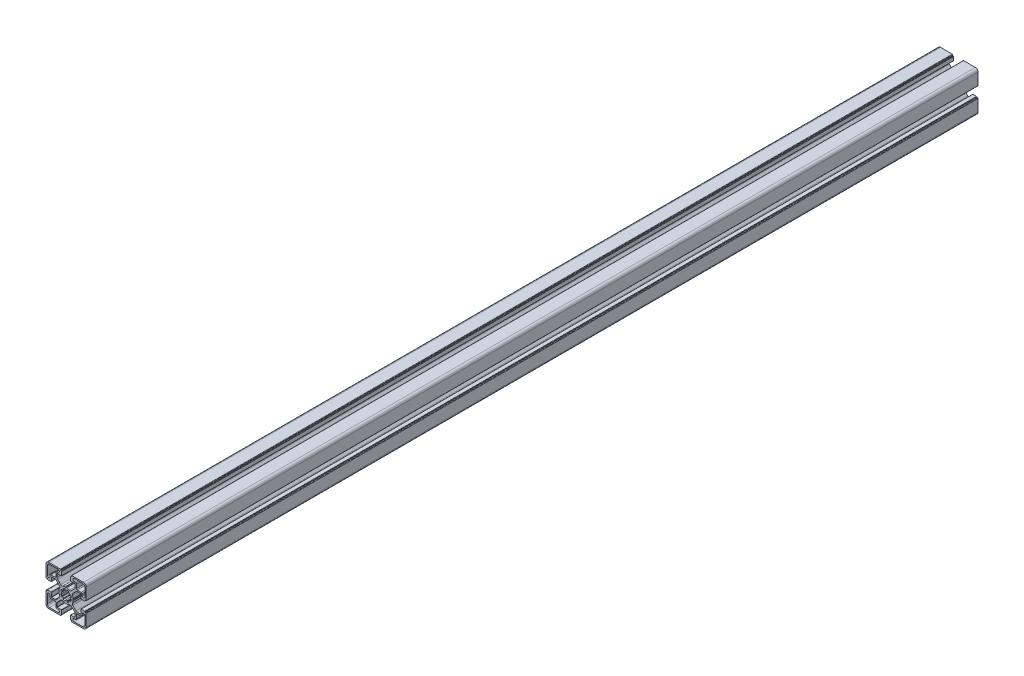
SolidWorks part; units mm, degrees
ref_plane "Plan de face" through (0, 0, 0) normal (0, 0, 1) x (1, 0, 0)
ref_plane "Plan de dessus" through (0, 0, 0) normal (0, 1, 0) x (1, 0, 0)
ref_plane "Plan de droite" through (0, 0, 0) normal (1, 0, 0) x (0, 0, -1)
sketch "Esquisse2" plane through (0, 0, 0) normal (0, 0, 1) x (1, 0, 0)
  line L28 (-195.0842, -352.0697) -> (-194.515, -352.1681)
  line L29 (-195.438, -354.39) -> (-195.9151, -354.0583)
  line L30 (-197.1408, -355.2803) -> (-196.8135, -355.7444)
  line L31 (-199.0372, -356.663) -> (-199.1374, -356.106)
  line L36 (-195.0842, -350.294) -> (-194.515, -350.1956)
  line L37 (-195.438, -347.9737) -> (-195.9151, -348.3053)
  line L38 (-197.1408, -347.0834) -> (-196.8135, -346.6192)
  line L39 (-199.0372, -345.7007) -> (-199.1374, -346.2577)
  line L40 (-200.9723, -356.663) -> (-200.8722, -356.106)
  line L41 (-202.8688, -355.2803) -> (-203.1961, -355.7444)
  line L42 (-204.5715, -354.39) -> (-204.0945, -354.0583)
  line L43 (-204.9253, -352.0697) -> (-205.4945, -352.1681)
  line L44 (-204.9253, -350.294) -> (-205.4945, -350.1956)
  line L45 (-204.5715, -347.9737) -> (-204.0945, -348.3053)
  line L46 (-202.8688, -347.0834) -> (-203.1961, -346.6192)
  line L47 (-200.9723, -345.7007) -> (-200.8722, -346.2577)
  line L105 (-200.0048, -338.2818) -> (-200.0048, -369.1677) construction
  line L107 (-190.0994, -351.1818) -> (-217.4619, -351.1818) construction
  line L108 (-191.0048, -330.1818) -> (-181.5048, -330.1818)
  line L109 (-189.4548, -333.1818) -> (-191.0048, -333.1818)
  line L116 (-221.0047, -332.6818) -> (-221.0047, -342.1816)
  line L117 (-218.0047, -342.1816) -> (-218.0047, -340.6318)
  line L118 (-217.0047, -339.6318) -> (-212.5547, -339.6318)
  line L119 (-211.5547, -338.6318) -> (-211.5547, -334.1818)
  line L120 (-210.5547, -333.1818) -> (-209.0047, -333.1818)
  line L121 (-209.0047, -330.1818) -> (-218.5047, -330.1818)
  line L122 (-188.4548, -338.6318) -> (-188.4548, -334.1818)
  line L123 (-183.0048, -339.6318) -> (-187.4548, -339.6318)
  line L124 (-182.0048, -342.1816) -> (-182.0048, -340.6318)
  line L125 (-179.0048, -332.6818) -> (-179.0048, -342.1816)
  line L126 (-191.0048, -372.1819) -> (-181.5048, -372.1819)
  line L127 (-189.4548, -369.1819) -> (-191.0048, -369.1819)
  line L128 (-188.4548, -363.7319) -> (-188.4548, -368.1819)
  line L129 (-183.0048, -362.7319) -> (-187.4548, -362.7319)
  line L130 (-182.0048, -360.182) -> (-182.0048, -361.7319)
  line L131 (-179.0048, -369.6819) -> (-179.0048, -360.182)
  line L196 (-192.4647, -351.135) -> (-192.0308, -350.3893)
  line L197 (-192.4413, -345.3231) -> (-188.875, -341.7569)
  line L198 (-187.5, -341.1873) -> (-183.6879, -341.1873)
  line L199 (-183.4879, -341.3873) -> (-183.4879, -345.9818)
  line L200 (-183.2879, -346.1818) -> (-179.2852, -346.1818)
  line L201 (-178.9852, -345.8818) -> (-178.9852, -345.6818)
  line L202 (-178.6852, -345.3818) -> (-178.0048, -345.3818)
  line L203 (-177.5048, -344.8818) -> (-177.5048, -331.6818)
  line L204 (-180.5048, -328.6818) -> (-193.6291, -328.6818)
  line L205 (-194.1291, -329.1818) -> (-194.1291, -329.8818)
  line L206 (-194.4291, -330.1818) -> (-194.7048, -330.1818)
  line L207 (-195.0048, -330.4818) -> (-195.0048, -334.515)
  line L208 (-194.8048, -334.715) -> (-190.0994, -334.715)
  line L209 (-189.8994, -334.915) -> (-189.8994, -338.7103)
  line L210 (-190.4852, -340.1245) -> (-194.0599, -343.6992)
  line L211 (-199.25, -343.207) -> (-199.8921, -343.5749)
  line L212 (-200.1174, -343.5749) -> (-200.7595, -343.207)
  line L213 (-205.9497, -343.6992) -> (-209.5244, -340.1245)
  line L214 (-210.1102, -338.7103) -> (-210.1102, -334.915)
  line L215 (-209.9102, -334.715) -> (-205.2048, -334.715)
  line L216 (-205.0048, -334.515) -> (-205.0048, -330.4818)
  line L217 (-205.3048, -330.1818) -> (-205.5805, -330.1818)
  line L218 (-205.8805, -329.8818) -> (-205.8805, -329.1818)
  line L219 (-206.3805, -328.6818) -> (-219.5047, -328.6818)
  line L220 (-222.5047, -331.6818) -> (-222.5047, -344.8818)
  line L221 (-222.0047, -345.3818) -> (-221.3244, -345.3818)
  line L222 (-221.0244, -345.6818) -> (-221.0244, -345.8818)
  line L223 (-220.7244, -346.1818) -> (-216.7217, -346.1818)
  line L224 (-216.5217, -345.9818) -> (-216.5217, -341.3873)
  line L225 (-216.3217, -341.1873) -> (-212.5095, -341.1873)
  line L226 (-211.1345, -341.7569) -> (-207.5682, -345.3231)
  line L227 (-207.9787, -350.3893) -> (-207.5448, -351.135)
  line L228 (-207.5448, -351.2287) -> (-207.9787, -351.9744)
  line L229 (-207.5682, -357.0405) -> (-211.1345, -360.6068)
  line L230 (-212.5095, -361.1764) -> (-216.3217, -361.1764)
  line L231 (-216.5217, -360.9764) -> (-216.5217, -356.3819)
  line L232 (-216.7217, -356.1819) -> (-220.7244, -356.1819)
  line L233 (-221.0244, -356.4819) -> (-221.0244, -356.6818)
  line L234 (-221.3244, -356.9818) -> (-222.0047, -356.9818)
  line L235 (-222.5047, -357.4818) -> (-222.5047, -370.6819)
  line L236 (-219.5047, -373.6819) -> (-206.3805, -373.6819)
  line L237 (-205.8805, -373.1819) -> (-205.8805, -372.4819)
  line L238 (-205.5805, -372.1819) -> (-205.3048, -372.1819)
  line L239 (-205.0048, -371.8819) -> (-205.0048, -367.8487)
  line L240 (-205.2048, -367.6487) -> (-209.9102, -367.6487)
  line L241 (-210.1102, -367.4487) -> (-210.1102, -363.6534)
  line L242 (-209.5244, -362.2392) -> (-205.9497, -358.6645)
  line L243 (-200.7595, -359.1566) -> (-200.1174, -358.7888)
  line L244 (-199.8921, -358.7888) -> (-199.25, -359.1566)
  line L245 (-194.0599, -358.6645) -> (-190.4852, -362.2392)
  line L246 (-189.8994, -363.6534) -> (-189.8994, -367.4487)
  line L247 (-190.0994, -367.6487) -> (-194.8048, -367.6487)
  line L248 (-195.0048, -367.8487) -> (-195.0048, -371.8819)
  line L249 (-194.7048, -372.1819) -> (-194.4291, -372.1819)
  line L250 (-194.1291, -372.4819) -> (-194.1291, -373.1819)
  line L251 (-193.6291, -373.6819) -> (-180.5048, -373.6819)
  line L252 (-177.5048, -370.6819) -> (-177.5048, -357.4818)
  line L253 (-178.0048, -356.9818) -> (-178.6852, -356.9818)
  line L254 (-178.9852, -356.6818) -> (-178.9852, -356.4819)
  line L255 (-179.2852, -356.1819) -> (-183.2879, -356.1819)
  line L256 (-183.4879, -356.3819) -> (-183.4879, -360.9764)
  line L257 (-183.6879, -361.1764) -> (-187.5, -361.1764)
  line L258 (-188.875, -360.6068) -> (-192.4413, -357.0405)
  line L259 (-192.0308, -351.9744) -> (-192.4647, -351.2287)
  line L260 (-209.0047, -372.1819) -> (-218.5047, -372.1819)
  line L261 (-210.5547, -369.1819) -> (-209.0047, -369.1819)
  line L262 (-211.5547, -363.7319) -> (-211.5547, -368.1819)
  line L263 (-217.0047, -362.7319) -> (-212.5547, -362.7319)
  line L264 (-218.0047, -360.182) -> (-218.0047, -361.7319)
  line L265 (-221.0047, -369.6819) -> (-221.0047, -360.182)
  arc A63 (-194.515, -352.1681) -> (-194.0979, -352.793) centre (-194.5809, -352.6637) cw
  arc A64 (-194.0979, -352.793) -> (-194.7023, -354.2383) centre (-199.9813, -351.1818) cw
  arc A65 (-194.7023, -354.2383) -> (-195.438, -354.39) centre (-195.1368, -353.9909) cw
  arc A66 (-195.9151, -354.0583) -> (-197.1408, -355.2803) centre (-200.0048, -351.1818) cw
  arc A67 (-196.8135, -355.7444) -> (-196.9604, -356.4813) centre (-197.2105, -356.0483) cw
  arc A68 (-196.9604, -356.4813) -> (-198.4097, -357.0759) centre (-199.9813, -351.1818) cw
  arc A69 (-198.4097, -357.0759) -> (-199.0372, -356.663) centre (-198.5421, -356.5938) cw
  arc A70 (-199.1374, -356.106) -> (-200.8722, -356.106) centre (-200.0048, -351.1818) cw
  arc A71 (-201.5998, -357.0759) -> (-200.9723, -356.663) centre (-201.4675, -356.5938) ccw
  arc A81 (-195.0842, -352.0697) -> (-195.0842, -350.294) centre (-200.0048, -351.1818) ccw
  arc A82 (-194.515, -350.1956) -> (-194.0979, -349.5706) centre (-194.5809, -349.7) ccw
  arc A83 (-194.0979, -349.5706) -> (-194.7023, -348.1254) centre (-199.9813, -351.1818) ccw
  arc A84 (-194.7023, -348.1254) -> (-195.438, -347.9737) centre (-195.1368, -348.3728) ccw
  arc A85 (-195.9151, -348.3053) -> (-197.1408, -347.0834) centre (-200.0048, -351.1818) ccw
  arc A86 (-196.8135, -346.6192) -> (-196.9604, -345.8824) centre (-197.2105, -346.3153) ccw
  arc A87 (-196.9604, -345.8824) -> (-198.4097, -345.2878) centre (-199.9813, -351.1818) ccw
  arc A88 (-198.4097, -345.2878) -> (-199.0372, -345.7007) centre (-198.5421, -345.7699) ccw
  arc A89 (-199.1374, -346.2577) -> (-200.8722, -346.2577) centre (-200.0048, -351.1818) ccw
  arc A90 (-203.0492, -356.4813) -> (-201.5998, -357.0759) centre (-200.0282, -351.1818) ccw
  arc A91 (-203.1961, -355.7444) -> (-203.0492, -356.4813) centre (-202.799, -356.0483) ccw
  arc A92 (-204.0945, -354.0583) -> (-202.8688, -355.2803) centre (-200.0048, -351.1818) ccw
  arc A93 (-205.3073, -354.2383) -> (-204.5715, -354.39) centre (-204.8728, -353.9909) ccw
  arc A94 (-205.9116, -352.793) -> (-205.3073, -354.2383) centre (-200.0282, -351.1818) ccw
  arc A95 (-205.4945, -352.1681) -> (-205.9116, -352.793) centre (-205.4286, -352.6637) ccw
  arc A96 (-204.9253, -352.0697) -> (-204.9253, -350.294) centre (-200.0048, -351.1818) cw
  arc A97 (-205.4945, -350.1956) -> (-205.9116, -349.5706) centre (-205.4286, -349.7) cw
  arc A98 (-205.9116, -349.5706) -> (-205.3073, -348.1254) centre (-200.0282, -351.1818) cw
  arc A99 (-205.3073, -348.1254) -> (-204.5715, -347.9737) centre (-204.8728, -348.3728) cw
  arc A100 (-204.0945, -348.3053) -> (-202.8688, -347.0834) centre (-200.0048, -351.1818) cw
  arc A101 (-203.1961, -346.6192) -> (-203.0492, -345.8824) centre (-202.799, -346.3153) cw
  arc A102 (-203.0492, -345.8824) -> (-201.5998, -345.2878) centre (-200.0282, -351.1818) cw
  arc A103 (-201.5998, -345.2878) -> (-200.9723, -345.7007) centre (-201.4675, -345.7699) cw
  arc A128 (-181.5048, -330.1818) -> (-179.0048, -332.6818) centre (-181.5048, -332.6818) cw
  arc A129 (-191.0048, -333.1818) -> (-191.0048, -330.1818) centre (-191.0048, -331.6818) cw
  arc A130 (-189.4548, -333.1818) -> (-188.4548, -334.1818) centre (-189.4548, -334.1818) cw
  arc A131 (-187.4548, -339.6318) -> (-188.4548, -338.6318) centre (-187.4548, -338.6318) cw
  arc A132 (-183.0048, -339.6318) -> (-182.0048, -340.6318) centre (-183.0048, -340.6318) cw
  arc A133 (-179.0048, -342.1816) -> (-182.0048, -342.1816) centre (-180.5048, -342.1816) cw
  arc A140 (-221.0047, -342.1816) -> (-218.0047, -342.1816) centre (-219.5047, -342.1816) ccw
  arc A141 (-217.0047, -339.6318) -> (-218.0047, -340.6318) centre (-217.0047, -340.6318) ccw
  arc A142 (-212.5547, -339.6318) -> (-211.5547, -338.6318) centre (-212.5547, -338.6318) ccw
  arc A143 (-210.5547, -333.1818) -> (-211.5547, -334.1818) centre (-210.5547, -334.1818) ccw
  arc A144 (-209.0047, -333.1818) -> (-209.0047, -330.1818) centre (-209.0047, -331.6818) ccw
  arc A145 (-218.5047, -330.1818) -> (-221.0047, -332.6818) centre (-218.5047, -332.6818) ccw
  arc A146 (-191.0048, -369.1819) -> (-191.0048, -372.1819) centre (-191.0048, -370.6819) ccw
  arc A147 (-189.4548, -369.1819) -> (-188.4548, -368.1819) centre (-189.4548, -368.1819) ccw
  arc A148 (-187.4548, -362.7319) -> (-188.4548, -363.7319) centre (-187.4548, -363.7319) ccw
  arc A149 (-183.0048, -362.7319) -> (-182.0048, -361.7319) centre (-183.0048, -361.7319) ccw
  arc A150 (-179.0048, -360.182) -> (-182.0048, -360.182) centre (-180.5048, -360.182) ccw
  arc A151 (-181.5048, -372.1819) -> (-179.0048, -369.6819) centre (-181.5048, -369.6819) ccw
  arc A152 (-218.5047, -372.1819) -> (-221.0047, -369.6819) centre (-218.5047, -369.6819) cw
  arc A153 (-209.0047, -369.1819) -> (-209.0047, -372.1819) centre (-209.0047, -370.6819) cw
  arc A154 (-210.5547, -369.1819) -> (-211.5547, -368.1819) centre (-210.5547, -368.1819) cw
  arc A155 (-212.5547, -362.7319) -> (-211.5547, -363.7319) centre (-212.5547, -363.7319) cw
  arc A156 (-217.0047, -362.7319) -> (-218.0047, -361.7319) centre (-217.0047, -361.7319) cw
  arc A157 (-221.0047, -360.182) -> (-218.0047, -360.182) centre (-219.5047, -360.182) cw
  arc A254 (-192.4647, -351.135) -> (-192.4734, -351.1818) centre (-192.2739, -351.1948) ccw
  arc A255 (-192.0308, -350.3893) -> (-192.0048, -350.2678) centre (-192.2037, -350.2887) ccw
  arc A256 (-192.0048, -350.2678) -> (-192.8044, -347.57) centre (-199.9552, -351.157) ccw
  arc A257 (-192.4413, -345.3231) -> (-192.8044, -347.57) centre (-191.0663, -346.6981) ccw
  arc A258 (-187.5, -341.1873) -> (-188.875, -341.7569) centre (-187.5, -343.1318) ccw
  arc A259 (-183.4879, -341.3873) -> (-183.6879, -341.1873) centre (-183.6879, -341.3873) ccw
  arc A260 (-183.4879, -345.9818) -> (-183.2879, -346.1818) centre (-183.2879, -345.9818) ccw
  arc A261 (-179.2852, -346.1818) -> (-178.9852, -345.8818) centre (-179.2852, -345.8818) ccw
  arc A262 (-178.6852, -345.3818) -> (-178.9852, -345.6818) centre (-178.6852, -345.6818) ccw
  arc A263 (-178.0048, -345.3818) -> (-177.5048, -344.8818) centre (-178.0048, -344.8818) ccw
  arc A264 (-177.5048, -331.6818) -> (-180.5048, -328.6818) centre (-180.5048, -331.6818) ccw
  arc A265 (-193.6291, -328.6818) -> (-194.1291, -329.1818) centre (-193.6291, -329.1818) ccw
  arc A266 (-194.4291, -330.1818) -> (-194.1291, -329.8818) centre (-194.4291, -329.8818) ccw
  arc A267 (-194.7048, -330.1818) -> (-195.0048, -330.4818) centre (-194.7048, -330.4818) ccw
  arc A268 (-195.0048, -334.515) -> (-194.8048, -334.715) centre (-194.8048, -334.515) ccw
  arc A269 (-189.8994, -334.915) -> (-190.0994, -334.715) centre (-190.0994, -334.915) ccw
  arc A270 (-190.4852, -340.1245) -> (-189.8994, -338.7103) centre (-191.8994, -338.7103) ccw
  arc A271 (-196.3383, -344.0086) -> (-194.0599, -343.6992) centre (-195.4193, -342.2322) ccw
  arc A272 (-196.3383, -344.0086) -> (-199.1284, -343.1818) centre (-199.9813, -351.1818) ccw
  arc A273 (-199.1284, -343.1818) -> (-199.25, -343.207) centre (-199.1506, -343.3806) ccw
  arc A274 (-200.0048, -343.6509) -> (-199.8921, -343.5749) centre (-200.0537, -343.457) ccw
  arc A275 (-200.1174, -343.5749) -> (-200.0048, -343.6509) centre (-199.9559, -343.457) ccw
  arc A276 (-200.7595, -343.207) -> (-200.8812, -343.1818) centre (-200.8589, -343.3806) ccw
  arc A277 (-200.8812, -343.1818) -> (-203.6713, -344.0086) centre (-200.0282, -351.1818) ccw
  arc A278 (-205.9497, -343.6992) -> (-203.6713, -344.0086) centre (-204.5903, -342.2322) ccw
  arc A279 (-210.1102, -338.7103) -> (-209.5244, -340.1245) centre (-208.1102, -338.7103) ccw
  arc A280 (-209.9102, -334.715) -> (-210.1102, -334.915) centre (-209.9102, -334.915) ccw
  arc A281 (-205.2048, -334.715) -> (-205.0048, -334.515) centre (-205.2048, -334.515) ccw
  arc A282 (-205.0048, -330.4818) -> (-205.3048, -330.1818) centre (-205.3048, -330.4818) ccw
  arc A283 (-205.8805, -329.8818) -> (-205.5805, -330.1818) centre (-205.5805, -329.8818) ccw
  arc A284 (-205.8805, -329.1818) -> (-206.3805, -328.6818) centre (-206.3805, -329.1818) ccw
  arc A285 (-219.5047, -328.6818) -> (-222.5047, -331.6818) centre (-219.5047, -331.6818) ccw
  arc A286 (-222.5047, -344.8818) -> (-222.0047, -345.3818) centre (-222.0047, -344.8818) ccw
  arc A287 (-221.0244, -345.6818) -> (-221.3244, -345.3818) centre (-221.3244, -345.6818) ccw
  arc A288 (-221.0244, -345.8818) -> (-220.7244, -346.1818) centre (-220.7244, -345.8818) ccw
  arc A289 (-216.7217, -346.1818) -> (-216.5217, -345.9818) centre (-216.7217, -345.9818) ccw
  arc A290 (-216.3217, -341.1873) -> (-216.5217, -341.3873) centre (-216.3217, -341.3873) ccw
  arc A291 (-211.1345, -341.7569) -> (-212.5095, -341.1873) centre (-212.5095, -343.1318) ccw
  arc A292 (-207.2051, -347.57) -> (-207.5682, -345.3231) centre (-208.9432, -346.6981) ccw
  arc A293 (-207.2051, -347.57) -> (-208.0048, -350.2678) centre (-200.0543, -351.157) ccw
  arc A294 (-208.0048, -350.2678) -> (-207.9787, -350.3893) centre (-207.8059, -350.2887) ccw
  arc A295 (-207.5361, -351.1818) -> (-207.5448, -351.135) centre (-207.7357, -351.1948) ccw
  arc A296 (-207.5448, -351.2287) -> (-207.5361, -351.1818) centre (-207.7357, -351.1689) ccw
  arc A297 (-207.9787, -351.9744) -> (-208.0048, -352.0959) centre (-207.8059, -352.075) ccw
  arc A298 (-208.0048, -352.0959) -> (-207.2051, -354.7937) centre (-200.0543, -351.2067) ccw
  arc A299 (-207.5682, -357.0405) -> (-207.2051, -354.7937) centre (-208.9432, -355.6656) ccw
  arc A300 (-212.5095, -361.1764) -> (-211.1345, -360.6068) centre (-212.5095, -359.2319) ccw
  arc A301 (-216.5217, -360.9764) -> (-216.3217, -361.1764) centre (-216.3217, -360.9764) ccw
  arc A302 (-216.5217, -356.3819) -> (-216.7217, -356.1819) centre (-216.7217, -356.3819) ccw
  arc A303 (-220.7244, -356.1819) -> (-221.0244, -356.4819) centre (-220.7244, -356.4819) ccw
  arc A304 (-221.3244, -356.9818) -> (-221.0244, -356.6818) centre (-221.3244, -356.6818) ccw
  arc A305 (-222.0047, -356.9818) -> (-222.5047, -357.4818) centre (-222.0047, -357.4818) ccw
  arc A306 (-222.5047, -370.6819) -> (-219.5047, -373.6819) centre (-219.5047, -370.6819) ccw
  arc A307 (-206.3805, -373.6819) -> (-205.8805, -373.1819) centre (-206.3805, -373.1819) ccw
  arc A308 (-205.5805, -372.1819) -> (-205.8805, -372.4819) centre (-205.5805, -372.4819) ccw
  arc A309 (-205.3048, -372.1819) -> (-205.0048, -371.8819) centre (-205.3048, -371.8819) ccw
  arc A310 (-205.0048, -367.8487) -> (-205.2048, -367.6487) centre (-205.2048, -367.8487) ccw
  arc A311 (-210.1102, -367.4487) -> (-209.9102, -367.6487) centre (-209.9102, -367.4487) ccw
  arc A312 (-209.5244, -362.2392) -> (-210.1102, -363.6534) centre (-208.1102, -363.6534) ccw
  arc A313 (-203.6713, -358.3551) -> (-205.9497, -358.6645) centre (-204.5903, -360.1315) ccw
  arc A314 (-203.6713, -358.3551) -> (-200.8812, -359.1819) centre (-200.0282, -351.1818) ccw
  arc A315 (-200.8812, -359.1819) -> (-200.7595, -359.1566) centre (-200.8589, -358.9831) ccw
  arc A316 (-200.0048, -358.7128) -> (-200.1174, -358.7888) centre (-199.9559, -358.9067) ccw
  arc A317 (-199.8921, -358.7888) -> (-200.0048, -358.7128) centre (-200.0537, -358.9067) ccw
  arc A318 (-199.25, -359.1566) -> (-199.1284, -359.1819) centre (-199.1506, -358.9831) ccw
  arc A319 (-199.1284, -359.1819) -> (-196.3383, -358.3551) centre (-199.9813, -351.1818) ccw
  arc A320 (-194.0599, -358.6645) -> (-196.3383, -358.3551) centre (-195.4193, -360.1315) ccw
  arc A321 (-189.8994, -363.6534) -> (-190.4852, -362.2392) centre (-191.8994, -363.6534) ccw
  arc A322 (-190.0994, -367.6487) -> (-189.8994, -367.4487) centre (-190.0994, -367.4487) ccw
  arc A323 (-194.8048, -367.6487) -> (-195.0048, -367.8487) centre (-194.8048, -367.8487) ccw
  arc A324 (-195.0048, -371.8819) -> (-194.7048, -372.1819) centre (-194.7048, -371.8819) ccw
  arc A325 (-194.1291, -372.4819) -> (-194.4291, -372.1819) centre (-194.4291, -372.4819) ccw
  arc A326 (-194.1291, -373.1819) -> (-193.6291, -373.6819) centre (-193.6291, -373.1819) ccw
  arc A327 (-180.5048, -373.6819) -> (-177.5048, -370.6819) centre (-180.5048, -370.6819) ccw
  arc A328 (-177.5048, -357.4818) -> (-178.0048, -356.9818) centre (-178.0048, -357.4818) ccw
  arc A329 (-178.9852, -356.6818) -> (-178.6852, -356.9818) centre (-178.6852, -356.6818) ccw
  arc A330 (-178.9852, -356.4819) -> (-179.2852, -356.1819) centre (-179.2852, -356.4819) ccw
  arc A331 (-183.2879, -356.1819) -> (-183.4879, -356.3819) centre (-183.2879, -356.3819) ccw
  arc A332 (-183.6879, -361.1764) -> (-183.4879, -360.9764) centre (-183.6879, -360.9764) ccw
  arc A333 (-188.875, -360.6068) -> (-187.5, -361.1764) centre (-187.5, -359.2319) ccw
  arc A334 (-192.8044, -354.7937) -> (-192.4413, -357.0405) centre (-191.0663, -355.6656) ccw
  arc A335 (-192.8044, -354.7937) -> (-192.0048, -352.0959) centre (-199.9552, -351.2067) ccw
  arc A336 (-192.0048, -352.0959) -> (-192.0308, -351.9744) centre (-192.2037, -352.075) ccw
  arc A337 (-192.4734, -351.1818) -> (-192.4647, -351.2287) centre (-192.2739, -351.1689) ccw
extrude "Boss.-Extru.1" add sketch "Esquisse2" along normal blind 1000
